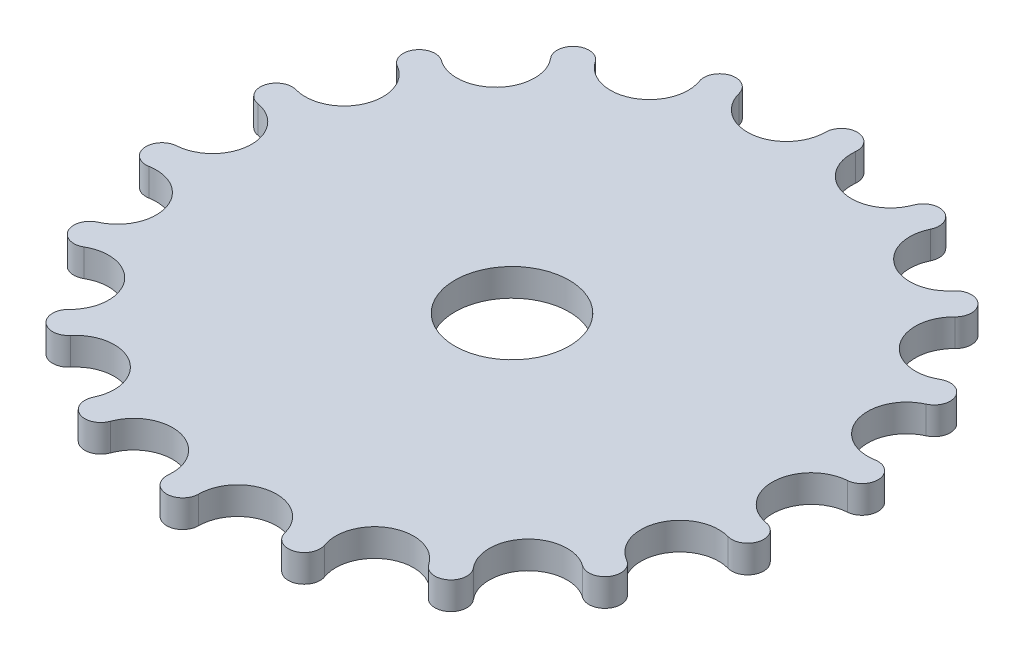
SolidWorks part; units mm, degrees
ref_plane "Front Plane" through (0, 0, 0) normal (0, 0, 1) x (1, 0, 0)
ref_plane "Top Plane" through (0, 0, 0) normal (0, 1, 0) x (1, 0, 0)
ref_plane "Right Plane" through (0, 0, 0) normal (1, 0, 0) x (0, 0, -1)
sketch "Sketch1" plane through (0, 0, 0) normal (0, 1, 0) x (1, 0, 0)
  line L6 (0, -38.1) -> (0, 0) construction
  line L7 (0, 0) -> (13.031, -35.8023) construction
  circle A0 centre (0, 0) radius 6.604
  circle A1 centre (0, 0) radius 38.1 construction
  circle A21 centre (0, 0) radius 31.75 construction
  arc A22 (0, -36.2089) -> (8.8631, -35.1074) centre (4.5, -36.2089) cw
  arc A23 (8.8631, -35.1074) -> (12.3842, -34.0252) centre (10.6512, -34.656) ccw
  circle A24 centre (0, 0) radius 36.2089 construction
  arc A25 (-3.6788, -36.0215) -> (0, -36.2089) centre (-1.8442, -36.2089) ccw
  arc A26 (-12.3842, -34.0252) -> (-3.6788, -36.0215) centre (-8.1555, -35.5643) cw
  arc A27 (-15.7771, -32.5909) -> (-12.3842, -34.0252) centre (-14.1171, -33.3945) ccw
  arc A28 (-23.2746, -27.7376) -> (-15.7771, -32.5909) centre (-19.8274, -30.6302) cw
  arc A29 (-25.9723, -25.2294) -> (-23.2746, -27.7376) centre (-24.6873, -26.5522) ccw
  arc A30 (-31.3578, -18.1044) -> (-25.9723, -25.2294) centre (-29.1078, -22.0016) cw
  arc A31 (-33.035, -14.8248) -> (-31.3578, -18.1044) centre (-32.2799, -16.5073) ccw
  arc A32 (-35.6588, -6.2876) -> (-33.035, -14.8248) centre (-34.8774, -10.7192) cw
  arc A33 (-36.1131, -2.6321) -> (-35.6588, -6.2876) centre (-35.979, -4.4714) ccw
  arc A34 (-35.6588, 6.2876) -> (-36.1131, -2.6321) centre (-36.4402, 1.856) cw
  arc A35 (-34.8354, 9.878) -> (-35.6588, 6.2876) centre (-35.3385, 8.1038) ccw
  arc A36 (-31.3578, 18.1044) -> (-34.8354, 9.878) centre (-33.6078, 14.2073) cw
  arc A37 (-29.3561, 21.1967) -> (-31.3578, 18.1044) centre (-30.4357, 19.7016) ccw
  arc A38 (-23.2746, 27.7376) -> (-29.3561, 21.1967) centre (-26.7218, 24.8451) cw
  arc A39 (-20.336, 29.9588) -> (-23.2746, 27.7376) centre (-21.8619, 28.923) ccw
  arc A40 (-12.3842, 34.0252) -> (-20.336, 29.9588) centre (-16.6128, 32.4861) cw
  arc A41 (-8.8631, 35.1074) -> (-12.3842, 34.0252) centre (-10.6512, 34.656) ccw
  arc A42 (0, 36.2089) -> (-8.8631, 35.1074) centre (-4.5, 36.2089) cw
  arc A43 (3.6788, 36.0215) -> (0, 36.2089) centre (1.8442, 36.2089) ccw
  arc A44 (12.3842, 34.0252) -> (3.6788, 36.0215) centre (8.1555, 35.5643) cw
  arc A45 (15.7771, 32.5909) -> (12.3842, 34.0252) centre (14.1171, 33.3945) ccw
  arc A46 (23.2746, 27.7376) -> (15.7771, 32.5909) centre (19.8274, 30.6302) cw
  arc A47 (25.9723, 25.2294) -> (23.2746, 27.7376) centre (24.6873, 26.5522) ccw
  arc A48 (31.3578, 18.1044) -> (25.9723, 25.2294) centre (29.1078, 22.0016) cw
  arc A49 (33.035, 14.8248) -> (31.3578, 18.1044) centre (32.2799, 16.5073) ccw
  arc A50 (35.6588, 6.2876) -> (33.035, 14.8248) centre (34.8774, 10.7192) cw
  arc A51 (36.1131, 2.6321) -> (35.6588, 6.2876) centre (35.979, 4.4714) ccw
  arc A52 (35.6588, -6.2876) -> (36.1131, 2.6321) centre (36.4402, -1.856) cw
  arc A53 (34.8354, -9.878) -> (35.6588, -6.2876) centre (35.3385, -8.1038) ccw
  arc A54 (31.3578, -18.1044) -> (34.8354, -9.878) centre (33.6078, -14.2073) cw
  arc A55 (29.3561, -21.1967) -> (31.3578, -18.1044) centre (30.4357, -19.7016) ccw
  arc A56 (23.2746, -27.7376) -> (29.3561, -21.1967) centre (26.7218, -24.8451) cw
  arc A57 (20.336, -29.9588) -> (23.2746, -27.7376) centre (21.8619, -28.923) ccw
  arc A58 (12.3842, -34.0252) -> (20.336, -29.9588) centre (16.6128, -32.4861) cw
  point P101 (0, 0)
  point P102 (0, 0)
  dimension "D2" = 76.2
  dimension "D3" = 63.5
  dimension "D5" = 4.5
  dimension "D6" = 18
  dimension "D1" = 13.208
  dimension "D4" = 20
extrude "Boss-Extrude1" add sketch "Sketch1" along normal blind 3.175
